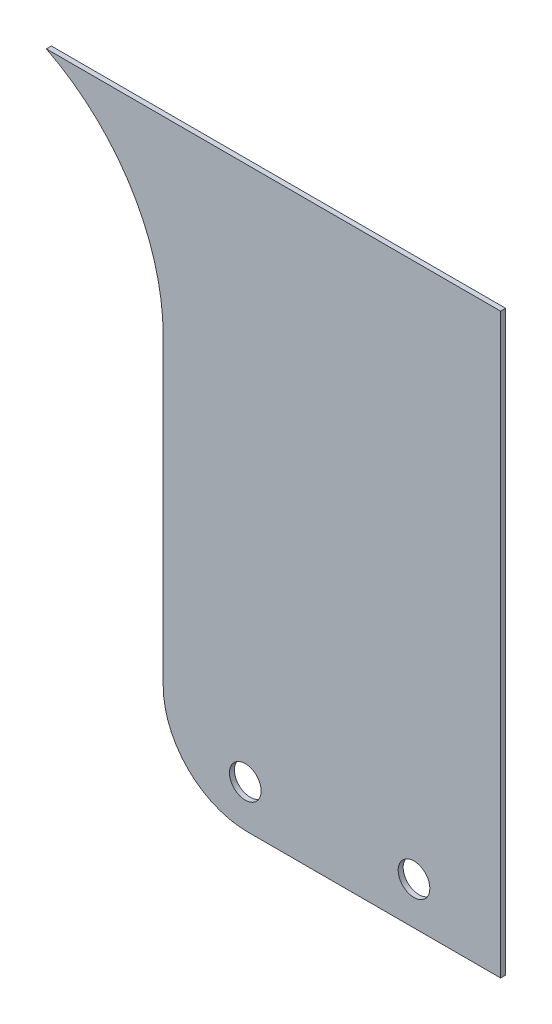
SolidWorks part; units mm, degrees
ref_plane "Front Plane" through (0, 0, 0) normal (0, 0, 1) x (1, 0, 0)
ref_plane "Top Plane" through (0, 0, 0) normal (0, 1, 0) x (1, 0, 0)
ref_plane "Right Plane" through (0, 0, 0) normal (1, 0, 0) x (0, 0, -1)
sketch "Sketch1" plane through (0, 0, 165.1) normal (0, 0, 1) x (1, 0, 0)
  line L0 (-418.175, 962.43) -> (-584.2, 962.43) construction
  line L1 (-418.175, 962.43) -> (-554.9557, 962.43)
  line L2 (-418.175, 962.43) -> (-418.175, 788.53)
  line L3 (-418.175, 788.53) -> (-494.375, 788.53)
  line L4 (-519.775, 813.93) -> (-519.775, 905.0248)
  line L5 (-375.1, 788.53) -> (-418.175, 788.53) construction
  line L6 (-584.2, 905.0248) -> (-519.775, 905.0248) construction
  line L9 (-490.3, 812.8) -> (-490.3, 780) construction
  arc A0 (-519.775, 905.0248) -> (-554.9557, 962.43) centre (-584.2, 905.0248) ccw
  circle A1 centre (-444.2625, 801.23) radius 4.7625
  circle A2 centre (-495.0625, 801.23) radius 4.7625
  arc A6 (-494.375, 788.53) -> (-519.775, 813.93) centre (-494.375, 813.93) cw
  point P25 (-519.775, 788.53)
  dimension "D3" = 25.4
  dimension "D5" = 9.525
  dimension "D6" = 9.525
  dimension "D1" = 101.6
  dimension "D2" = 173.9
  dimension "D4" = 50.8
  dimension "D7" = 50.8
  dimension "D8" = 12.7
  dimension "D9" = 12.7
  dimension "D10" = 24.7125
extrude "Extrude1" add sketch "Sketch1" along normal blind 1.5
